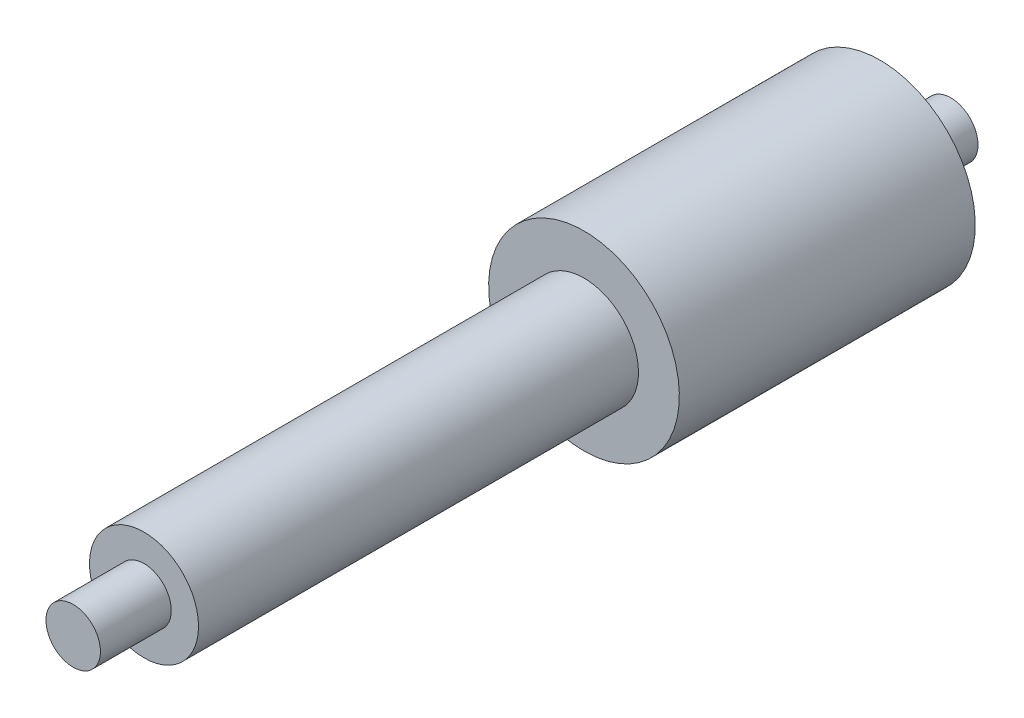
SolidWorks part; units mm, degrees
material "Сталь ШХ15 ГОСТ 801-78"
ref_plane "Plane1" through (0, 0, 0) normal (0, 0, 1) x (1, 0, 0)
ref_plane "Plane2" through (0, 0, 0) normal (0, 1, 0) x (1, 0, 0)
ref_plane "Plane3" through (0, 0, 0) normal (1, 0, 0) x (0, 0, -1)
sketch "Эскиз1" plane through (0, 0, 0) normal (0, 0, 1) x (1, 0, 0)
  circle A0 centre (0, 0) radius 2
  dimension "D1" = 4
extrude "Бобышка-Вытянуть1" add sketch "Эскиз1" against normal up to surface (27.0135 mm away) from surface contours A0
sketch "Эскиз2" plane through (0, 0, 30.4) normal (0, 0, 1) x (1, 0, 0)
  circle A0 centre (0, 0) radius 1
  dimension "D1" = 2
extrude "Бобышка-Вытянуть2" add sketch "Эскиз2" along normal up to surface (2.6 mm away) contours A0
sketch "Эскиз4" plane through (0, 0, 3.3865) normal (0, 0, -1) x (-1, 0, 0)
  circle A0 centre (0, 0) radius 1
  dimension "D1" = 2
extrude "Бобышка-Вытянуть3" add sketch "Эскиз4" along normal up to surface (2.6 mm away)
sketch "Эскиз6" plane through (0, 0, 3.3865) normal (0, 0, -1) x (-1, 0, 0)
  circle A0 centre (0, 0) radius 3.5
  dimension "D1" = 7
extrude "Бобышка-Вытянуть5" add sketch "Эскиз6" along normal up to surface (10.8635 mm away) from surface at -10.8635
